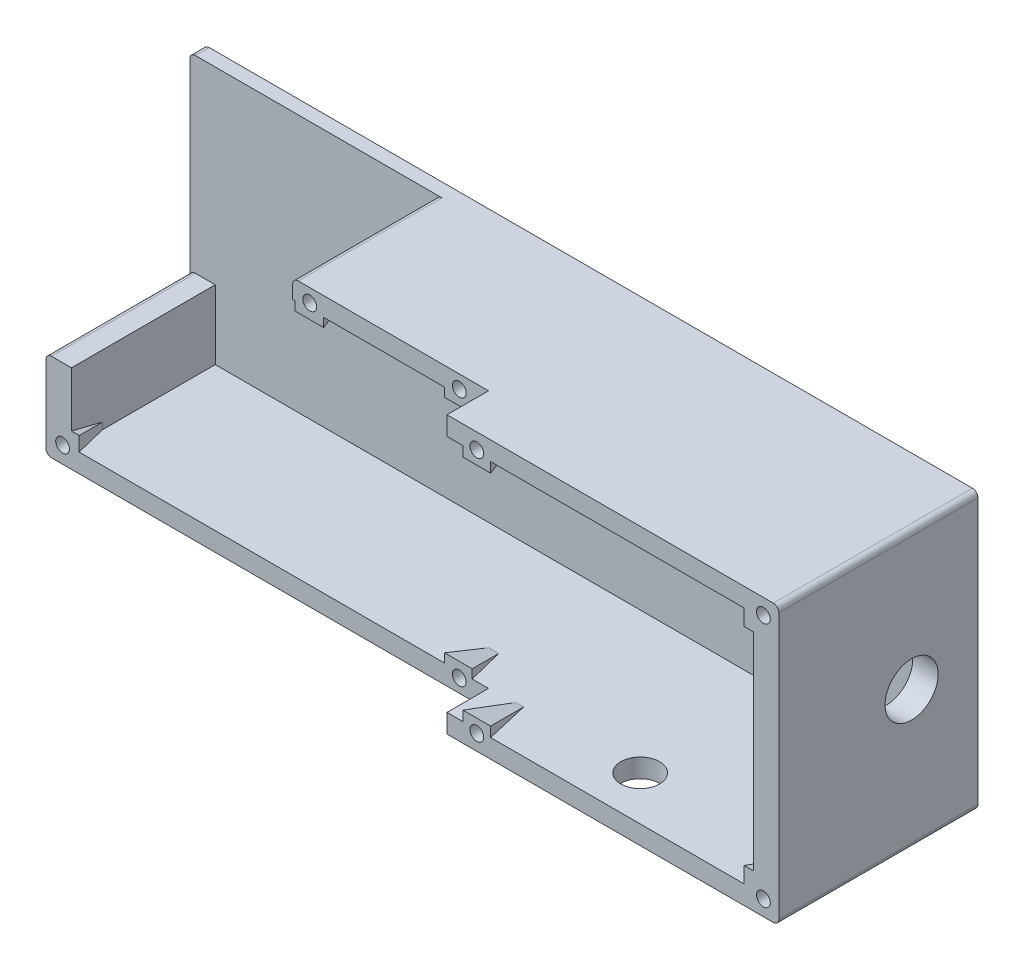
SolidWorks part; units mm, degrees
ref_plane "Front Plane" through (0, 0, 0) normal (0, 0, 1) x (1, 0, 0)
ref_plane "Top Plane" through (0, 0, 0) normal (0, 1, 0) x (1, 0, 0)
ref_plane "Right Plane" through (0, 0, 0) normal (1, 0, 0) x (0, 0, -1)
sketch "Sketch1" plane through (0, 0, 0) normal (0, 0, 1) x (1, 0, 0)
  line L1 (88.9, -31.75) -> (-88.9, -31.75)
  line L2 (88.9, -31.75) -> (88.9, 31.75)
  line L3 (88.9, 31.75) -> (-88.9, 31.75)
  line L4 (-88.9, -31.75) -> (-88.9, 31.75)
  line L5 (88.9, -31.75) -> (-88.9, 31.75) construction
  line L6 (88.9, 31.75) -> (-88.9, -31.75) construction
  point P0 (0, 0)
  dimension "D1" = 177.8
  dimension "D2" = 63.5
extrude "Boss-Extrude1" add sketch "Sketch1" along normal blind 45.72
sketch "Sketch2" plane through (0, 0, 45.72) normal (0, 0, 1) x (1, 0, 0)
  line L0 (-88.9, -31.75) -> (88.9, -31.75) construction
  line L1 (-88.9, 31.75) -> (12.7, 31.75)
  line L2 (-88.9, 31.75) -> (-88.9, -31.75)
  line L3 (-88.9, -31.75) -> (12.7, -31.75)
  line L4 (12.7, 31.75) -> (12.7, -31.75)
  line L5 (88.9, -31.75) -> (88.9, 31.75) construction
  dimension "D1" = 76.2
extrude "Cut-Extrude1" cut sketch "Sketch2" against normal blind 9.525
sketch "Sketch3" plane through (0, 0, 45.72) normal (0, 0, 1) x (1, 0, 0)
  line L1 (83.058, -27.432) -> (-83.058, -27.432)
  line L2 (83.058, -27.432) -> (83.058, 27.432)
  line L3 (83.058, 27.432) -> (-83.058, 27.432)
  line L4 (-83.058, -27.432) -> (-83.058, 27.432)
  line L5 (83.058, -27.432) -> (-83.058, 27.432) construction
  line L6 (83.058, 27.432) -> (-83.058, -27.432) construction
  point P0 (0, 0)
  dimension "D1" = 54.864
  dimension "D2" = 166.116
extrude "Cut-Extrude2" cut sketch "Sketch3" against normal blind 42.545
sketch "Sketch4" plane through (88.9, 0, 0) normal (1, 0, 0) x (0, 0, -1)
  line L0 (0, -31.75) -> (0, 31.75) construction
  line L1 (-45.72, -31.75) -> (0, -31.75) construction
  circle A0 centre (-15.24, 0) radius 6.096
  dimension "D1" = 12.192
  dimension "D2" = 15.24
  dimension "D3" = 31.75
extrude "Cut-Extrude3" cut sketch "Sketch4" against normal blind 31.75
sketch "Sketch5" plane through (0, 31.75, 0) normal (0, 1, 0) x (1, 0, 0)
  line L0 (88.9, -45.72) -> (12.7, -45.72) construction
  circle A0 centre (46.9009, -35.56) radius 4.445
  dimension "D1" = 8.89
  dimension "D2" = 10.16
extrude "Cut-Extrude4" cut sketch "Sketch5" against normal blind 31.75 from offset 43.18 offset against normal yes
sketch "Sketch9" plane through (0, 0, 36.195) normal (0, 0, 1) x (1, 0, 0)
  line L0 (12.7, 31.75) -> (-88.9, 31.75) construction
  line L1 (8.9601, 31.75) -> (2.6101, 31.75)
  line L2 (8.9601, 31.75) -> (8.9601, 25.4)
  line L3 (8.9601, 25.4) -> (2.6101, 25.4)
  line L4 (2.6101, 31.75) -> (2.6101, 25.4)
  line L5 (-88.9, -31.75) -> (12.7, -31.75) construction
  line L6 (-25.1304, 31.75) -> (-31.6957, 31.75)
  line L7 (-25.1304, 31.75) -> (-25.1304, 25.4)
  line L8 (-25.1304, 25.4) -> (-31.6957, 25.4)
  line L9 (-31.6957, 31.75) -> (-31.6957, 25.4)
  line L10 (8.9601, -31.75) -> (2.6101, -31.75)
  line L11 (8.9601, -31.75) -> (8.9601, -25.4)
  line L12 (8.9601, -25.4) -> (2.6101, -25.4)
  line L13 (2.6101, -31.75) -> (2.6101, -25.4)
  line L15 (-88.9, -31.75) -> (-81.28, -31.75)
  line L16 (-88.9, -31.75) -> (-88.9, -24.13)
  line L17 (-88.9, -24.13) -> (-81.28, -24.13)
  line L18 (-81.28, -31.75) -> (-81.28, -24.13)
  dimension "D1" = 6.35
  dimension "D2" = 6.35
  dimension "D3" = 6.35
  dimension "D4" = 0
  dimension "D5" = 6.35
  dimension "D6" = 6.35
  dimension "D8" = 7.62
  dimension "D9" = 7.62
extrude "Boss-Extrude2" add sketch "Sketch9" against normal blind 10.16 draft 14
sketch "Sketch6" plane through (0, 0, 36.195) normal (0, 0, 1) x (1, 0, 0)
  line L0 (8.9601, -27.432) -> (12.7, -27.432) construction
  line L1 (-88.9, 31.75) -> (-32.258, 31.75)
  line L2 (-88.9, 31.75) -> (-88.9, -11.557)
  line L3 (-88.9, -11.557) -> (-32.258, -11.557)
  line L4 (-32.258, 31.75) -> (-32.258, -11.557)
  line L5 (-83.058, 27.432) -> (-83.058, -24.13) construction
  dimension "D1" = 15.875
  dimension "D2" = 50.8
extrude "Cut-Extrude5" cut sketch "Sketch6" against normal blind 33.02
sketch "Sketch8" plane through (0, 0, 36.195) normal (0, 0, 1) x (1, 0, 0)
  line L0 (12.7, 31.75) -> (-32.258, 31.75) construction
  line L1 (-88.9, -31.75) -> (12.7, -31.75) construction
  line L2 (-87.63, -31.75) -> (12.7, -31.75) construction
  line L4 (-88.9, -11.557) -> (-88.9, -31.75) construction
  circle A0 centre (5.9963, 28.702) radius 1.5875
  circle A1 centre (-28.3407, 28.702) radius 1.5875
  circle A2 centre (5.9963, -28.702) radius 1.5875
  circle A3 centre (-85.09, -27.94) radius 1.5875
  point P16 (-88.9, -28.4479)
  dimension "D2" = 3.175
  dimension "D3" = 3.175
  dimension "D5" = 3.175
  dimension "D6" = 3.175
  dimension "D7" = 3.81
  dimension "D1" = 3.048
  dimension "D4" = 3.048
  dimension "D8" = 3.81
  dimension "D9" = 3.048
extrude "Cut-Extrude7" cut sketch "Sketch8" against normal blind 4.572
fillet "Fillet1" radius 1.27 4 edges at (-32.258, 31.75, 19.685) (-88.9, -31.75, 18.0975) (88.9, -31.75, 22.86) (88.9, 31.75, 22.86)
fillet "Fillet2" radius 1.27 1 edges at (-88.9, -11.557, 19.685)
sketch "Sketch10" plane through (0, 0, 45.72) normal (0, 0, 1) x (1, 0, 0)
  line L0 (87.63, 31.75) -> (12.7, 31.75) construction
  line L1 (16.3634, 31.75) -> (22.7134, 31.75)
  line L2 (16.3634, 31.75) -> (16.3634, 25.146)
  line L3 (16.3634, 25.146) -> (22.7134, 25.146)
  line L4 (22.7134, 31.75) -> (22.7134, 25.146)
  line L5 (12.7, -31.75) -> (87.63, -31.75) construction
  line L6 (88.528, 31.378) -> (80.908, 31.378)
  line L7 (88.528, 31.378) -> (88.528, 23.758)
  line L8 (88.528, 23.758) -> (80.908, 23.758)
  line L9 (80.908, 31.378) -> (80.908, 23.758)
  line L10 (88.528, -31.378) -> (80.908, -31.378)
  line L11 (88.528, -31.378) -> (88.528, -23.758)
  line L12 (88.528, -23.758) -> (80.908, -23.758)
  line L13 (80.908, -31.378) -> (80.908, -23.758)
  line L14 (22.7134, -31.75) -> (16.3634, -31.75)
  line L15 (22.7134, -31.75) -> (22.7134, -25.146)
  line L16 (22.7134, -25.146) -> (16.3634, -25.146)
  line L17 (16.3634, -31.75) -> (16.3634, -25.146)
  arc A1 (88.9, 30.48) -> (87.63, 31.75) centre (87.63, 30.48) ccw construction
  arc A2 (87.63, -31.75) -> (88.9, -30.48) centre (87.63, -30.48) ccw construction
  dimension "D1" = 6.604
  dimension "D2" = 6.35
  dimension "D4" = 7.62
  dimension "D5" = 7.62
  dimension "D6" = 7.62
  dimension "D7" = 7.62
  dimension "D8" = 6.35
  dimension "D9" = 6.604
extrude "Boss-Extrude3" add sketch "Sketch10" against normal blind 10.16 draft 13
sketch "Sketch7" plane through (0, 0, 45.72) normal (0, 0, 1) x (1, 0, 0)
  line L0 (87.63, 31.75) -> (12.7, 31.75) construction
  line L1 (88.9, -30.48) -> (88.9, 30.48) construction
  line L2 (0, 0) -> (117.7158, 0) construction
  line L4 (52.9492, 27.432) -> (52.9492, -27.432) construction
  line L6 (87.63, 31.75) -> (12.7, 31.75) construction
  line L7 (22.7134, 25.146) -> (22.7134, 27.432) construction
  line L8 (16.3634, 27.432) -> (12.7, 27.432) construction
  line L9 (12.7, -27.432) -> (16.3634, -27.432) construction
  line L10 (105.8984, 0) -> (-11.8174, 0) construction
  line L11 (12.7, -31.75) -> (87.63, -31.75) construction
  circle A0 centre (85.344, 28.194) radius 1.5875
  circle A1 centre (85.344, -28.194) radius 1.5875
  circle A4 centre (19.5384, 28.194) radius 1.5875
  circle A5 centre (19.5384, -28.194) radius 1.5875
  dimension "D3" = 3.175
  dimension "D4" = 3.175
  dimension "D7" = 3.175
  dimension "D1" = 3.556
  dimension "D2" = 3.556
  dimension "D5" = 3.556
  dimension "D6" = 3.175
  dimension "D8" = 3.556
extrude "Cut-Extrude6" cut sketch "Sketch7" against normal blind 4.572
fillet "Fillet3" radius 1.27 1 edges at (-88.9, 31.75, 1.5875)
